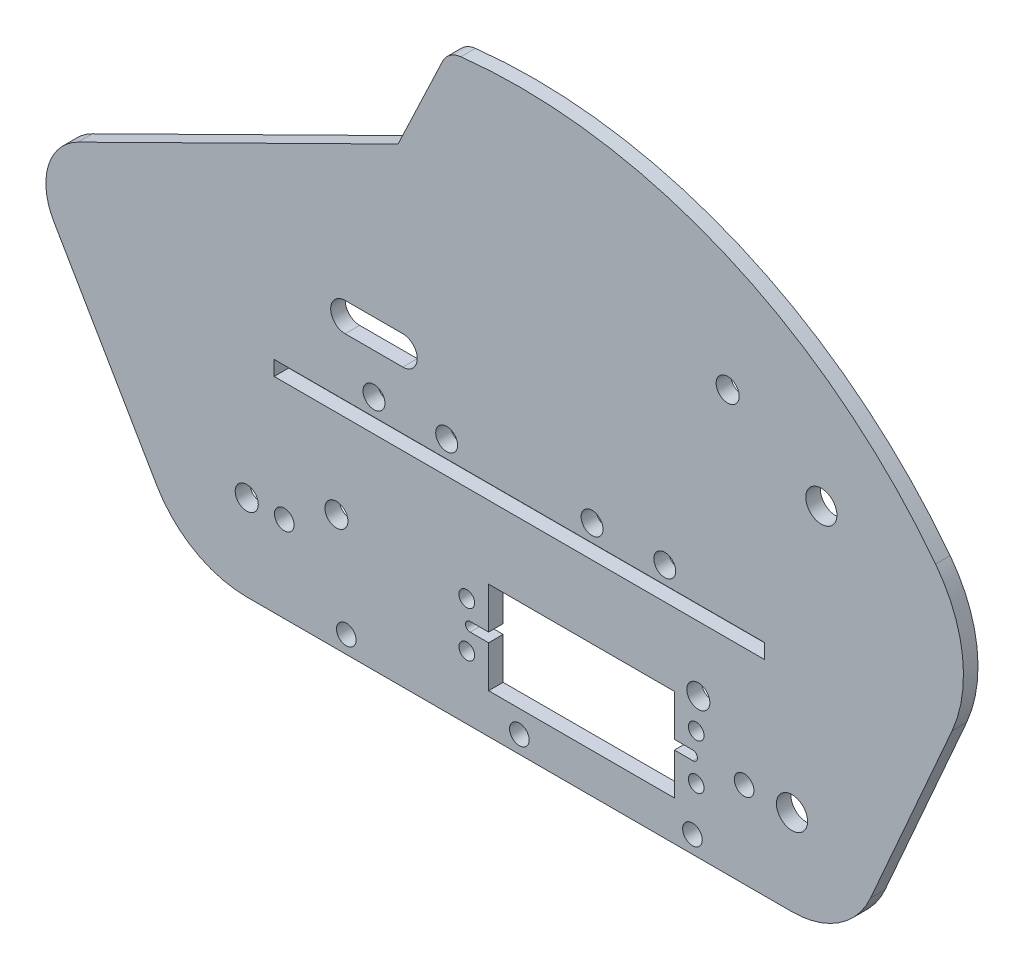
SolidWorks part; units mm, degrees
ref_plane "Front Plane" through (0, 0, 0) normal (0, 0, 1) x (1, 0, 0)
ref_plane "Top Plane" through (0, 0, 0) normal (0, 1, 0) x (1, 0, 0)
ref_plane "Right Plane" through (0, 0, 0) normal (1, 0, 0) x (0, 0, -1)
sketch "Sketch1" plane through (0, 0, 0) normal (0, 0, 1) x (1, 0, 0)
  line L8 (0, 18.9078) -> (120.015, 18.9078) construction
  line L18 (155.2575, 52.1157) -> (-35.2425, 52.1157) construction
  line L37 (0, 0) -> (120.015, 0)
  line L54 (155.2575, 52.1157) -> (137.3256, 11.3022)
  line L55 (60.0075, 52.1157) -> (60.0075, 18.9078) construction
  line L56 (-35.2425, 52.1157) -> (-17.3106, 11.3022)
  line L57 (0, 18.9078) -> (19.7347, 25.5664) construction
  line L59 (151.631, 82.096) -> (-31.616, 82.096) construction
  circle A21 centre (120.015, 18.9078) radius 3.429
  circle A22 centre (0, 18.9078) radius 2.54
  circle A24 centre (19.7347, 25.5664) radius 2.54
  arc A25 (137.3256, 11.3022) -> (120.015, 0) centre (120.015, 18.9078) cw
  arc A26 (0, 0) -> (-17.3106, 11.3022) centre (0, 18.9078) cw
  arc A28 (151.631, 82.096) -> (-31.616, 82.096) centre (60.0075, 11.7572) ccw
  arc A29 (151.631, 82.096) -> (155.2575, 52.1157) centre (128.1135, 64.0417) cw
  arc A30 (-31.616, 82.096) -> (-35.2425, 52.1157) centre (-8.0985, 64.0417) ccw
  dimension "D5" = 18.9078
  dimension "D8" = 183.2469
  dimension "D3" = 52.1157
  dimension "D11" = 6.858
  dimension "D10" = 5.08
  dimension "D1" = 190.5
  dimension "D4" = 18.645
  dimension "D6" = 20.8278
  dimension "D7" = 120.015
  dimension "D9" = 29.9803
extrude "Boss-Extrude1" add sketch "Sketch1" along normal blind 3.2004
sketch "Sketch2" plane through (0, 0, 0) normal (0, 0, -1) x (-1, 0, 0)
  line L1 (-155.2575, 52.1157) -> (35.2425, 52.1157) construction
  line L28 (-92.0115, 52.1157) -> (-76.0095, 52.1157) construction
  line L29 (-76.0095, 52.1157) -> (-44.0055, 52.1157) construction
  line L30 (-44.0055, 52.1157) -> (-28.0035, 52.1157) construction
  circle A0 centre (-92.0115, 52.1157) radius 2.413
  circle A1 centre (-76.0095, 52.1157) radius 2.413
  circle A2 centre (-44.0055, 52.1157) radius 2.413
  circle A3 centre (-28.0035, 52.1157) radius 2.413
  point P11 (-36.0045, 52.1157)
  point P16 (-84.0105, 52.1157)
  dimension "D3" = 4.826
  dimension "D2" = 16.002
  dimension "D4" = 48.006
extrude "Cut-Extrude1" cut sketch "Sketch2" against normal blind 3.2004
sketch "Sketch5" plane through (0, 0, 0) normal (0, 0, -1) x (-1, 0, 0)
  line L0 (0, 18.9078) -> (-120.015, 18.9078) construction
  line L5 (-73.682, 29.0678) -> (-73.682, 8.7478) construction
  line L6 (-53.235, 29.0678) -> (-53.235, 8.7478)
  line L10 (-94.129, 8.7478) -> (-94.129, 29.0678)
  line L13 (-98.932, 13.9078) -> (-98.932, 23.9078) construction
  line L14 (-48.432, 13.9078) -> (-48.432, 23.9078) construction
  line L15 (-98.932, 18.9078) -> (-48.432, 18.9078) construction
  line L21 (-94.129, 8.7478) -> (-53.235, 8.7478)
  line L25 (-94.129, 29.0678) -> (-53.235, 29.0678)
  circle A0 centre (-98.932, 23.9078) radius 1.7272
  circle A1 centre (-48.432, 13.9078) radius 1.7272
  circle A2 centre (-48.432, 23.9078) radius 1.7272
  circle A3 centre (-98.932, 13.9078) radius 1.7272
  circle A6 centre (-120.015, 18.9078) radius 3.429 construction
  point P0 (-83.532, 18.9078)
  point P1 (-120.015, 18.9078)
  point P4 (-73.682, 18.9078)
  dimension "D2" = 20.32
  dimension "D3" = 3.4544
  dimension "D1" = 50.5
  dimension "D4" = 40.894
  dimension "D5" = 15.4
  dimension "D6" = 10
extrude "Cut-Extrude3" cut sketch "Sketch5" against normal through all
sketch "Sketch7" plane through (0, 0, 0) normal (0, 0, -1) x (-1, 0, 0)
  line L0 (0, 18.9078) -> (-120.015, 18.9078) construction
  line L1 (-53.235, 8.7478) -> (-53.235, 29.0678) construction
  line L4 (-98.193, 19.9238) -> (-94.129, 19.9238)
  line L5 (-98.193, 19.9238) -> (-98.193, 17.8918) construction
  line L6 (-94.129, 29.0678) -> (-94.129, 8.7478) construction
  line L7 (-98.193, 17.8918) -> (-94.129, 17.8918)
  line L8 (-94.129, 19.9238) -> (-94.129, 17.8918)
  line L9 (-53.235, 19.9238) -> (-49.171, 19.9238)
  line L10 (-53.235, 19.9238) -> (-53.235, 17.8918)
  line L11 (-53.235, 17.8918) -> (-49.171, 17.8918)
  line L12 (-49.171, 19.9238) -> (-49.171, 17.8918) construction
  arc A6 (-49.171, 19.9238) -> (-49.171, 17.8918) centre (-49.171, 18.9078) cw
  arc A7 (-98.193, 19.9238) -> (-98.193, 17.8918) centre (-98.193, 18.9078) ccw
  point P22 (-94.129, 18.9078)
  point P23 (-53.235, 18.9078)
  dimension "D4" = 4.064
  dimension "D5" = 2.032
extrude "Cut-Extrude5" cut sketch "Sketch7" against normal up to surface (3.2004 mm away) up to face at (97.2048, 23.9078, 3.2004)
sketch "Sketch6" plane through (0, 0, 0) normal (0, 0, -1) x (-1, 0, 0)
  line L0 (-99.4008, 30.8094) -> (-120.015, 18.9078) construction
  line L1 (0, 0) -> (-120.015, 0) construction
  circle A1 centre (-19.7347, 25.5664) radius 2.54 construction
  circle A2 centre (-99.4008, 30.8094) radius 2.54
  circle A3 centre (-120.015, 18.9078) radius 3.429 construction
  dimension "D2" = 23.8032
  dimension "D3" = 30
extrude "Cut-Extrude4" cut sketch "Sketch6" against normal through all
sketch "Sketch8" plane through (0, 0, 3.2004) normal (0, 0, 1) x (1, 0, 0)
  line L0 (75.1019, 13.9078) -> (21.7621, 13.9078) construction
  line L1 (53.235, 8.7478) -> (53.235, 17.8918) construction
  circle A0 centre (48.432, 13.9078) radius 1.7272 construction
  point P2 (48.432, 13.9078)
sketch "Sketch9" plane through (0, 0, 3.2004) normal (0, 0, 1) x (1, 0, 0)
  line L0 (21.9075, 3.81) -> (98.1075, 3.81) construction
  line L1 (60.0075, 7.62) -> (60.0075, 0) construction
  line L2 (0, 0) -> (120.015, 0) construction
  circle A0 centre (21.9075, 3.81) radius 2.159
  circle A1 centre (60.0075, 3.81) radius 2.159
  circle A2 centre (98.1075, 3.81) radius 2.159
  point P6 (60.0075, 3.81)
  dimension "D3" = 4.318
  dimension "D1" = 76.2
  dimension "D2" = 7.62
extrude "Cut-Extrude6" cut sketch "Sketch9" against normal up to surface (3.2004 mm away) up to face at (96.8608, 30.8094, 0)
sketch "Sketch10" plane through (0, 0, 3.2004) normal (0, 0, 1) x (1, 0, 0)
  line L0 (60.0075, 55.9257) -> (60.0075, 52.1157) construction
  line L1 (6.0325, 81.3257) -> (113.9825, 81.3257) construction
  line L2 (6.0325, 81.3257) -> (6.0325, 55.9257) construction
  line L3 (6.0325, 55.9257) -> (113.9825, 55.9257) construction
  line L4 (113.9825, 81.3257) -> (113.9825, 55.9257) construction
  line L5 (155.2575, 52.1157) -> (-35.2425, 52.1157) construction
  line L6 (60.0075, 52.1157) -> (60.0075, 48.3057) construction
  line L7 (60.0075, 52.1157) -> (60.0075, 18.9078) construction
  line L8 (6.0325, 48.3057) -> (113.9825, 48.3057)
  line L9 (6.0325, 48.3057) -> (6.0325, 45.0545)
  line L10 (6.0325, 45.0545) -> (113.9825, 45.0545)
  line L11 (113.9825, 48.3057) -> (113.9825, 45.0545)
  dimension "D1" = 25.4
  dimension "D2" = 107.95
  dimension "D3" = 3.81
  dimension "D4" = 7.62
  dimension "D5" = 3.2512
extrude "Cut-Extrude7" cut sketch "Sketch10" against normal up to surface (3.2004 mm away) up to face at (19.7485, 3.81, 0)
sketch "Sketch11" plane through (0, 0, 3.2004) normal (0, 0, 1) x (1, 0, 0)
  line L0 (146.2916, 31.7089) -> (111.6995, 46.9073) construction
  line L1 (111.6995, 46.9073) -> (126.4745, 80.5358) construction
  line L2 (137.3256, 11.3022) -> (155.2575, 52.1157) construction
  line L3 (105.8603, 92.4374) -> (126.4745, 80.5358) construction
  line L5 (6.0325, 81.3257) -> (113.9825, 81.3257) construction
  circle A0 centre (126.4745, 80.5358) radius 3.429
  circle A1 centre (105.8603, 92.4374) radius 2.54
  circle A2 centre (120.015, 18.9078) radius 3.429 construction
  circle A5 centre (19.7347, 25.5664) radius 2.54 construction
  dimension "D1" = 37.7837
  dimension "D2" = 36.7311
  dimension "D3" = 23.8032
  dimension "D4" = 30
extrude "Cut-Extrude8" cut sketch "Sketch11" against normal up to surface (3.2004 mm away) up to face at (60.0075, 46.6801, 0)
sketch "Sketch12" plane through (0, 0, 3.2004) normal (0, 0, 1) x (1, 0, 0)
  line L0 (-32.6149, 80.7753) -> (-17.2714, 56.9367)
  line L1 (-17.2714, 56.9367) -> (38.7942, 93.0228)
  line L2 (38.7942, 93.0228) -> (47.3024, 126.5656)
  line L3 (0, 18.9078) -> (0, 56.9367) construction
  line L4 (0, 56.9367) -> (-17.2714, 56.9367) construction
  line L6 (0, 0) -> (120.015, 0) construction
  arc A1 (47.3024, 126.5656) -> (-32.6149, 80.7753) centre (60.0075, 11.7572) ccw
  circle A3 centre (0, 18.9078) radius 2.54 construction
  arc A4 (151.631, 82.096) -> (-31.616, 82.096) centre (60.0075, 11.7572) ccw construction
  dimension "D1" = 66.675
  dimension "D2" = 137
  dimension "D3" = 28.3497
  dimension "D4" = 38.0289
  dimension "D5" = 17.2714
sketch "Sketch13" plane through (0, 0, 3.2004) normal (0, 0, 1) x (1, 0, 0)
  line L1 (-37.7469, 127.2665) -> (90.0451, 127.2665)
  line L2 (-37.7469, 127.2665) -> (-37.7469, 55.9257)
  line L3 (-37.7469, 55.9257) -> (90.0451, 55.9257)
  line L4 (90.0451, 127.2665) -> (90.0451, 55.9257)
  line L5 (6.0325, 55.9257) -> (113.9825, 55.9257) construction
  arc A0 (151.631, 82.096) -> (-31.616, 82.096) centre (60.0075, 11.7572) ccw construction
  arc A1 (-31.616, 82.096) -> (-35.2425, 52.1157) centre (-8.0985, 64.0417) ccw construction
sketch "Sketch14" plane through (0, 0, 0) normal (0, 0, -1) x (-1, 0, 0)
  line L0 (-44.301, 126.1937) -> (-33.3012, 102.9934)
  line L1 (-33.3012, 102.9934) -> (25.9331, 73.6792)
  line L2 (25.9331, 73.6792) -> (30.6884, 83.288)
  arc A0 (31.616, 82.096) -> (-151.631, 82.096) centre (-60.0075, 11.7572) ccw construction
  arc A1 (-44.301, 126.1937) -> (30.6884, 83.288) centre (-60.0075, 11.7572) cw
  point P4 (0, 0)
  dimension "D1" = 25.6758
  dimension "D2" = 66.0911
  dimension "D3" = 1.5104
  dimension "D4" = 10.7212
  dimension "D5" = 86.3961
extrude "Cut-Extrude9" cut sketch "Sketch14" against normal up to surface (3.2004 mm away) up to face at (129.9035, 80.5358, 3.2004)
sketch "Sketch15" plane through (0, 0, 3.2004) normal (0, 0, 1) x (1, 0, 0)
  line L1 (0, 0) -> (120.015, 0) construction
  line L3 (8.255, 18.9078) -> (109.4765, 18.9078) construction
  line L4 (60.0075, 18.9078) -> (60.0075, 0) construction
  circle A2 centre (8.255, 18.9078) radius 2.159
  circle A3 centre (0, 18.9078) radius 2.54 construction
  circle A4 centre (120.015, 18.9078) radius 3.429 construction
  circle A5 centre (109.4765, 18.9078) radius 2.159
  dimension "D1" = 8.255
  dimension "D2" = 10.5385
  dimension "D3" = 4.318
  dimension "D5" = 18.9078
extrude "Cut-Extrude10" cut sketch "Sketch15" against normal up to surface (3.2004 mm away) up to face at (42.2482, 57.2901, 0)
sketch "Sketch16" plane through (0, 0, 3.2004) normal (0, 0, 1) x (1, 0, 0)
  line L0 (-45.0411, 54.7574) -> (-19.8272, 11.4052)
  line L1 (-42.0685, 81.7954) -> (-45.0411, 54.7574) construction
  line L2 (0, 0) -> (120.015, 0) construction
  line L3 (-19.8272, 11.4052) -> (0, 0) construction
  line L4 (-35.2425, 52.1157) -> (-17.3106, 11.3022) construction
  line L5 (-33.9498, 89.8783) -> (-25.9331, 73.6792)
  line L6 (-30.6884, 83.288) -> (-25.9331, 73.6792) construction
  arc A0 (-33.9498, 89.8783) -> (-42.0685, 81.7954) centre (58.563, -11.1634) ccw
  arc A1 (-42.0685, 81.7954) -> (-45.0411, 54.7574) centre (-25.2559, 66.2646) ccw
  arc A2 (-25.9331, 73.6792) -> (0, 0) centre (218.9164, 118.4561) ccw
  arc A4 (-19.8272, 11.4052) -> (0, 0) centre (0, 22.9368) ccw
  dimension "D1" = 50.1513
  dimension "D2" = 22.8735
  dimension "D3" = 6.464
  dimension "D4" = 27.2009
  dimension "D5" = 143.544
extrude "Boss-Extrude2" add sketch "Sketch16" against normal up to surface (3.2004 mm away) up to face at (6.096, 18.9078, 0)
fillet "Fillet1" radius 5.08 2 edges at (44.301, 126.1937, 1.6002) (-33.9498, 89.8783, 1.6002)
sketch "Sketch17" plane through (0, 0, 0) normal (0, 0, -1) x (-1, 0, 0)
  line L1 (-34.3535, 67.3557) -> (-21.6535, 67.3557)
  line L2 (-34.3535, 67.3557) -> (-34.3535, 61.0057) construction
  line L3 (-34.3535, 61.0057) -> (-21.6535, 61.0057)
  line L4 (-21.6535, 67.3557) -> (-21.6535, 61.0057) construction
  line L7 (0, 0) -> (-120.015, 0) construction
  arc A0 (-21.6535, 67.3557) -> (-21.6535, 61.0057) centre (-21.6535, 64.1807) cw
  arc A1 (-34.3535, 67.3557) -> (-34.3535, 61.0057) centre (-34.3535, 64.1807) ccw
  circle A5 centre (-28.0035, 52.1157) radius 2.413 construction
  dimension "D3" = 8.89
  dimension "D4" = 6.35
  dimension "D1" = 12.7
  dimension "D2" = 6.35
extrude "Cut-Extrude11" cut sketch "Sketch17" against normal up to surface (3.2004 mm away) up to face at (10.414, 18.9078, 3.2004)
sketch "Sketch18" plane through (0, 0, 0) normal (0, 0, -1) x (-1, 0, 0)
  line L0 (-33.3012, 102.9934) -> (25.9331, 73.6792) construction
  line L1 (25.9331, 73.6792) -> (45.393, 113.0011)
  line L2 (25.9331, 73.6792) -> (68.9069, 52.412)
  line L3 (68.9069, 52.412) -> (91.4141, 83.706)
  line L4 (45.393, 113.0011) -> (91.4141, 83.706)
  line L5 (25.9331, 73.6792) -> (30.8705, 83.656) construction
extrude "Cut-Extrude12" cut sketch "Sketch18" against normal up to surface (3.2004 mm away) up to face at (28.0035, 64.1807, 3.2004)
fillet "Fillet2" radius 12.7 1 edges at (-47.8829, 62.8165, 1.6002)
